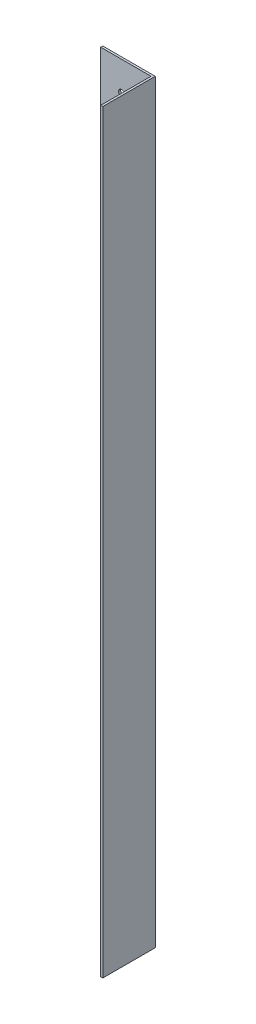
SolidWorks part; units mm, degrees
material "Aleación 1060"
ref_plane "Alzado" through (0, 0, 0) normal (0, 0, 1) x (1, 0, 0)
ref_plane "Planta" through (0, 0, 0) normal (0, 1, 0) x (1, 0, 0)
ref_plane "Vista lateral" through (0, 0, 0) normal (1, 0, 0) x (0, 0, -1)
sketch "Croquis1" plane through (0, 0, 0) normal (0, 0, 1) x (1, 0, 0)
  line L1 (-53.4017, 26.4852) -> (-29.4017, 26.4852)
  line L2 (-53.4017, 26.4852) -> (-53.4017, -333.5148)
  line L3 (-53.4017, -333.5148) -> (-29.4017, -333.5148)
  line L4 (-29.4017, 26.4852) -> (-29.4017, -333.5148)
  circle A0 centre (-43.4017, 12.4852) radius 1.5
  circle A1 centre (-43.4017, -319.5148) radius 1.5
  dimension "D6" = 10
  dimension "D1" = 24
  dimension "D2" = 360
  dimension "D3" = 14
  dimension "D4" = 14
  dimension "D5" = 10
sketch "Croquis2" plane through (0, 0, 0) normal (0, 0, 1) x (1, 0, 0)
  line L0 (-53.4017, -333.5148) -> (-29.4017, -333.5148) construction
  line L1 (-29.4017, 26.4852) -> (-28.4017, 26.4852)
  line L2 (-29.4017, 26.4852) -> (-29.4017, -333.5148)
  line L3 (-29.4017, -333.5148) -> (-28.4017, -333.5148)
  line L4 (-28.4017, 26.4852) -> (-28.4017, -333.5148)
  dimension "D1" = 1
extrude "Saliente-Extruir1" add sketch "Croquis1" along normal blind 1
extrude "Saliente-Extruir2" add sketch "Croquis2" along normal blind 25
